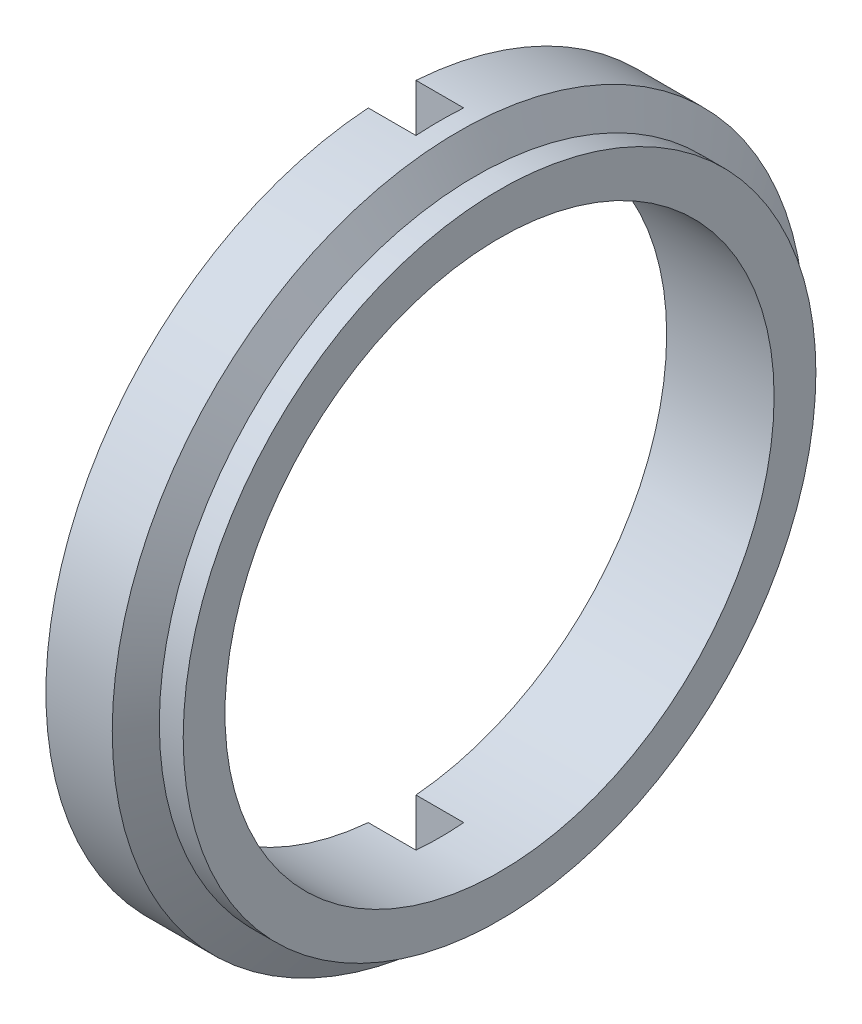
SolidWorks part; units mm, degrees
ref_plane "Front" through (0, 0, 0) normal (0, 0, 1) x (1, 0, 0)
ref_plane "Top" through (0, 0, 0) normal (0, 1, 0) x (1, 0, 0)
ref_plane "Right" through (0, 0, 0) normal (1, 0, 0) x (0, 0, -1)
sketch "Sketch1" plane through (0, 0, 0) normal (0, 0, 1) x (1, 0, 0)
  line L0 (0, 0) -> (-5.3991, 0) construction
  line L1 (0, 11.5) -> (-4.5, 11.5)
  line L2 (-4.5, 11.5) -> (-4.5, 14.5)
  line L3 (-4.5, 14.5) -> (-1.7217, 14.5)
  line L4 (-1.7217, 14.5) -> (-1, 13.25)
  line L5 (-1, 13.25) -> (0, 13.25)
  line L6 (0, 13.25) -> (0, 11.5)
  line L7 (-1, 13.25) -> (-1, 14.7873) construction
  dimension "D1" = 1.75
  dimension "D2" = 4.5
  dimension "D3" = 3
  dimension "D4" = 1
  dimension "D5" = 30
  dimension "D6" = 11.5
revolve "Base-Revolve" add sketch "Sketch1" angle 360 about L0
ref_plane "Plane1" through (-4.5, 0, 0) normal (-1, 0, 0) x (0, 0, 1)
sketch "Sketch2" plane through (-4.5, 0, 0) normal (-1, 0, 0) x (0, 0, 1)
  line L0 (-1, 14.8373) -> (1, 14.8373)
  line L1 (1, 14.8373) -> (1, -15.0577)
  line L2 (1, -15.0577) -> (-1, -15.0577)
  line L3 (-1, -15.0577) -> (-1, 14.8373)
  dimension "D1" = 2
  dimension "D2" = 2
  dimension "D3" = 1
extrude "Cut-Extrude1" cut sketch "Sketch2" against normal blind 2
